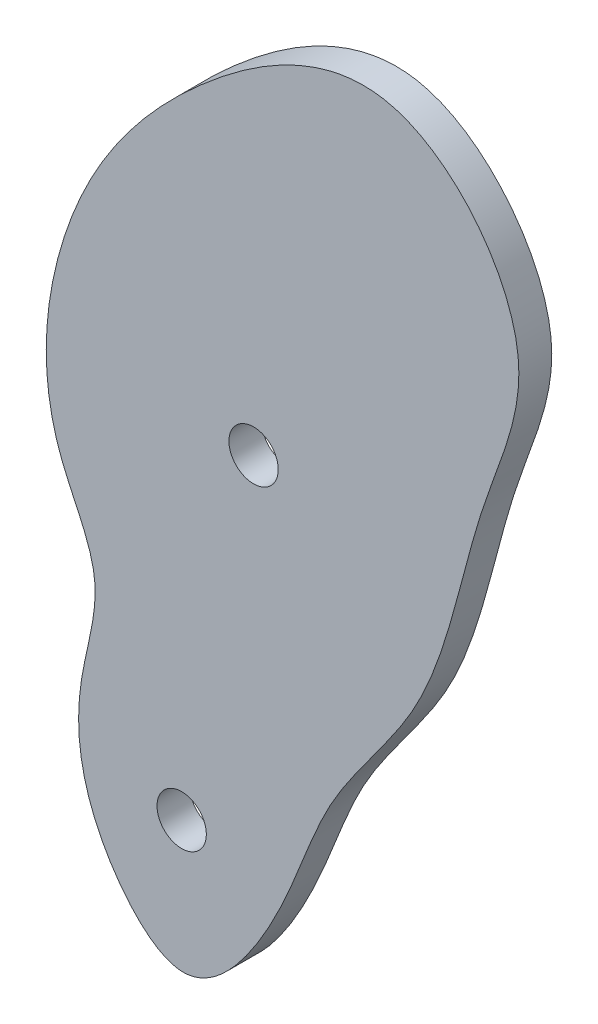
SolidWorks part; units mm, degrees
ref_plane "Front Plane" through (0, 0, 0) normal (0, 0, 1) x (1, 0, 0)
ref_plane "Top Plane" through (0, 0, 0) normal (0, 1, 0) x (1, 0, 0)
ref_plane "Right Plane" through (0, 0, 0) normal (1, 0, 0) x (0, 0, -1)
sketch "Sketch1" plane through (0, 0, 0) normal (0, 0, 1) x (1, 0, 0)
  line L0 (302.5, 350) -> (1512.5, 350) construction
  circle A0 centre (299.6639, 264.8473) radius 2.3813
  circle A1 centre (292.7229, 230.8861) radius 2.3813
  spline S0 degree 3 poles (283.3946, 225.7244) (281.9051, 236.3052) (285.7524, 247.1141) (278.5589, 258.0131) (280.2493, 276.5781) (292.0538, 293.0661) (313.3146, 306.2943) (328.645, 287.2657) (320.1969, 269.7136) (318.004, 252.9598) (305.9749, 239.7302) (303.0377, 227.7399) (293.4202, 214.6639) (283.3946, 225.7244) (281.9051, 236.3052) (285.7524, 247.1141) knots -0.174356 -0.116165 -0.068445 0 0.046533 0.091899 0.184135 0.30513 0.401871 0.499211 0.57086 0.681214 0.750348 0.825644 0.883835 0.931555 1 1.046533 1.091899 1.184135 only from (283.0551, 237.8271) to (283.0551, 237.8271)
  dimension "D1" = 4.7625
  dimension "D28" = 4.7625
  dimension "D2" = 281.072
  dimension "D3" = 281.3199
  dimension "D4" = 283.0551
  dimension "D5" = 284.2946
  dimension "D6" = 285.5341
  dimension "D7" = 292.7229
  dimension "D8" = 294.954
  dimension "D9" = 301.1512
  dimension "D10" = 307.3485
  dimension "D11" = 312.8022
  dimension "D12" = 315.0332
  dimension "D13" = 321.9742
  dimension "D14" = 325.1967
  dimension "D15" = 218.2436
  dimension "D16" = 224.4409
  dimension "D17" = 226.1762
  dimension "D18" = 237.8271
  dimension "D19" = 239.8102
  dimension "D20" = 246.9991
  dimension "D21" = 251.2132
  dimension "D22" = 255.4274
  dimension "D23" = 272.0361
  dimension "D24" = 273.7714
  dimension "D25" = 285.9181
  dimension "D26" = 293.6027
  dimension "D27" = 300.7916
extrude "Boss-Extrude1" add sketch "Sketch1" along normal blind 3.175
